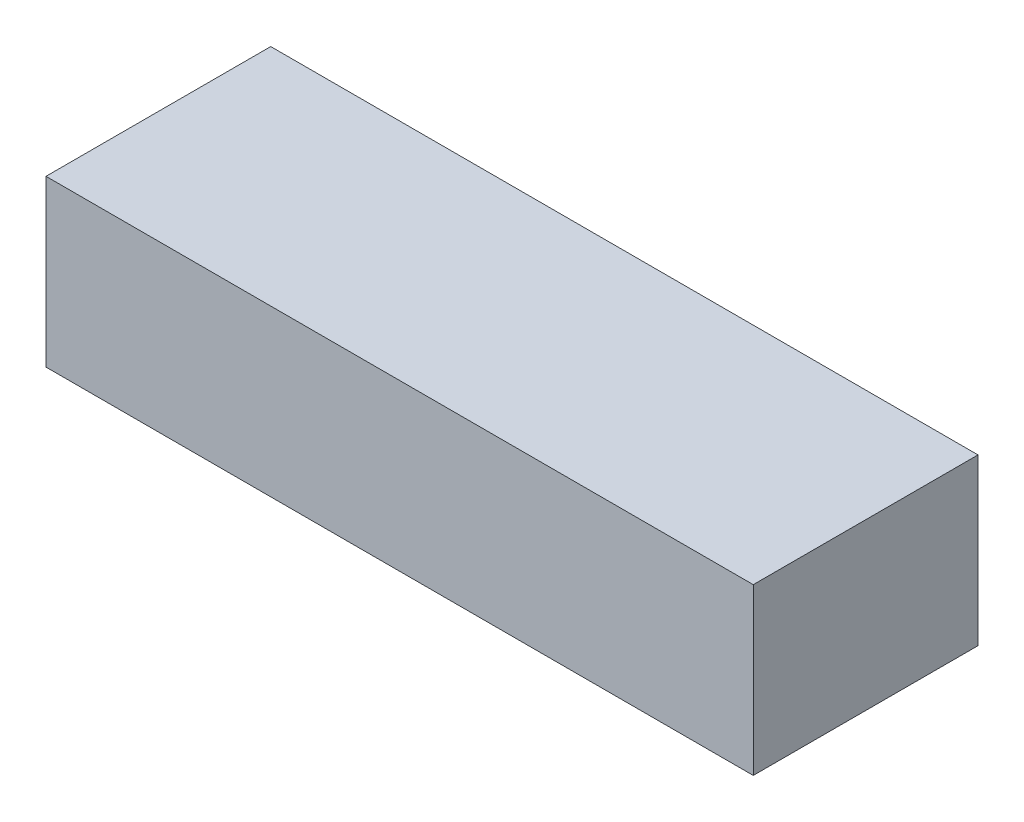
SolidWorks part; units mm, degrees
material "Thornel Mat VMA"
ref_plane "Front" through (0, 0, 0) normal (0, 0, 1) x (1, 0, 0)
ref_plane "Top" through (0, 0, 0) normal (0, 1, 0) x (1, 0, 0)
ref_plane "Right" through (0, 0, 0) normal (1, 0, 0) x (0, 0, -1)
sketch "Sketch1" plane through (0, 0, 0) normal (0, 1, 0) x (1, 0, 0)
  line L1 (-53.5, 17) -> (53.5, 17)
  line L2 (-53.5, 17) -> (-53.5, -17)
  line L3 (-53.5, -17) -> (53.5, -17)
  line L4 (53.5, 17) -> (53.5, -17)
  line L5 (-53.5, 17) -> (53.5, -17) construction
  line L6 (-53.5, -17) -> (53.5, 17) construction
  point P0 (0, 0)
  dimension "D1" = 107
  dimension "D2" = 34
extrude "Boss-Extrude1" add sketch "Sketch1" along normal blind 25
